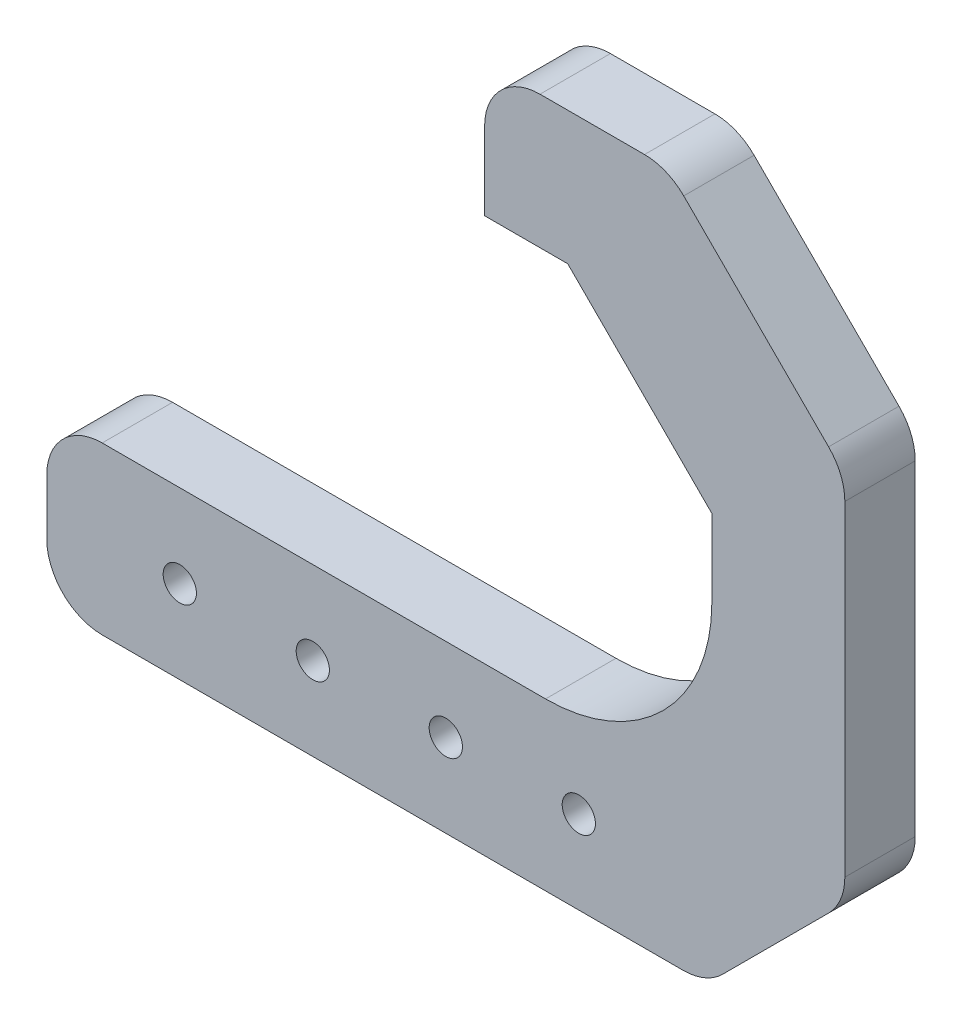
SolidWorks part; units mm, degrees
ref_plane "Front Plane" through (0, 0, 0) normal (0, 0, 1) x (1, 0, 0)
ref_plane "Top Plane" through (0, 0, 0) normal (0, 1, 0) x (1, 0, 0)
ref_plane "Right Plane" through (0, 0, 0) normal (1, 0, 0) x (0, 0, -1)
sketch "Sketch1" plane through (0, 0, 0) normal (0, 0, 1) x (1, 0, 0)
  line L1 (0, 0) -> (60, 0)
  line L2 (0, 0) -> (0, 15)
  line L3 (0, 15) -> (60, 15)
  line L4 (60, 0) -> (60, 15)
  line L5 (60, 0) -> (72, 0)
  line L6 (60, 0) -> (60, 50)
  line L7 (60, 50) -> (72, 50)
  line L8 (72, 0) -> (72, 50)
  line L9 (72, 50) -> (39.5, 50)
  line L10 (72, 50) -> (72, 62)
  line L11 (72, 62) -> (39.5, 62)
  line L12 (39.5, 50) -> (39.5, 62)
  circle A0 centre (48, 7.5) radius 1.5
  circle A1 centre (36, 7.5) radius 1.5
  circle A2 centre (24, 7.5) radius 1.5
  circle A3 centre (12, 7.5) radius 1.5
  dimension "D7" = 3
  dimension "D1" = 15
  dimension "D2" = 60
  dimension "D3" = 50
  dimension "D4" = 12
  dimension "D5" = 12
  dimension "D6" = 32.5
  dimension "D8" = 12
  dimension "D9" = 4
extrude "Boss-Extrude1" add sketch "Sketch1" along normal blind 6.35 contours L1 L4 L3 L2 A3 A2 A1 A0 | L5 L8 L7 L6 L4 | L12 L9 L7 L10 L11
fillet "Fillet1" radius 15 1 edges at (60, 15, 3.175)
chamfer "Chamfer1" distance 13 angle 45 1 edges at (60, 50, 3.175)
fillet "Fillet3" radius 5 1 edges at (39.5, 62, 3.175)
chamfer "Chamfer2" distance 12.5 angle 45 1 edges at (72, 0, 3.175)
chamfer "Chamfer3" distance 16 angle 45 1 edges at (72, 62, 3.175)
fillet "Fillet4" radius 5 4 edges at (59.5, 0, 3.175) (72, 12.5, 3.175) (72, 46, 3.175) (56, 62, 3.175)
fillet "Fillet5" radius 5 2 edges at (0, 15, 3.175) (0, 0, 3.175)
sketch "Sketch2" plane through (0, 0, 6.35) normal (0, 0, 1) x (1, 0, 0)
  line L0 (47, 50) -> (39.5, 50)
